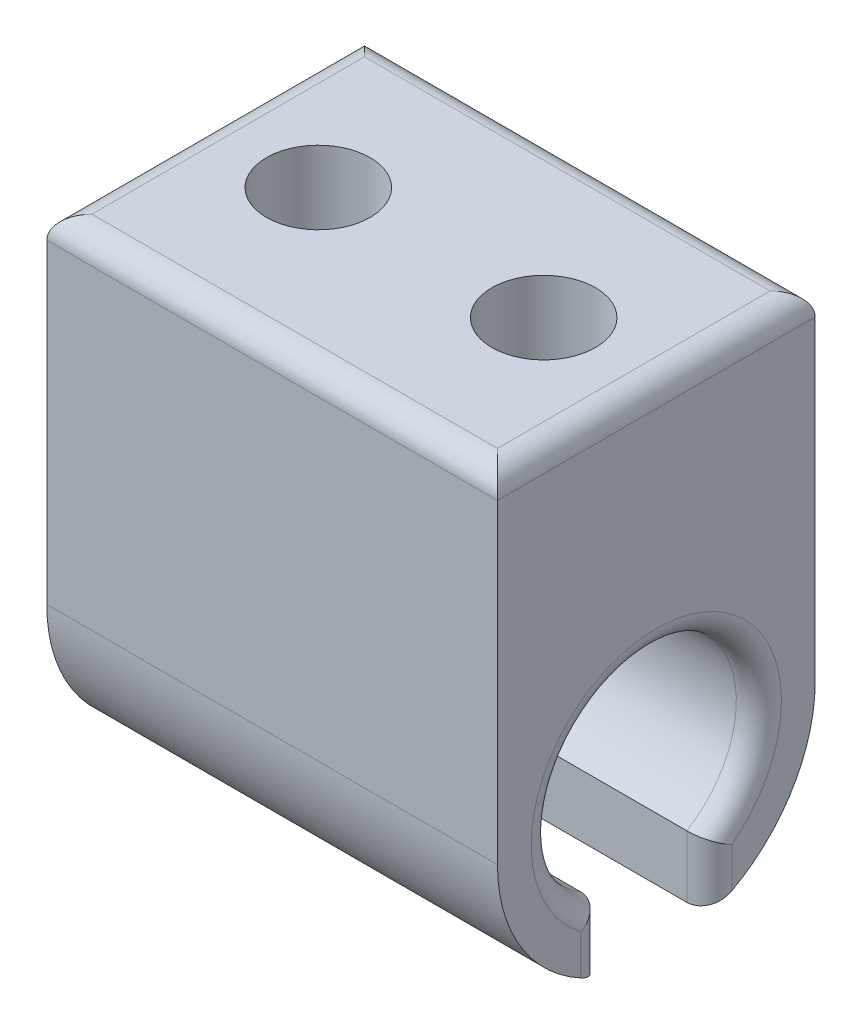
SolidWorks part; units mm, degrees
ref_plane "Front Plane" through (0, 0, 0) normal (0, 0, 1) x (1, 0, 0)
ref_plane "Top Plane" through (0, 0, 0) normal (0, 1, 0) x (1, 0, 0)
ref_plane "Right Plane" through (0, 0, 0) normal (1, 0, 0) x (0, 0, -1)
sketch "Sketch1" plane through (0, 0, 0) normal (1, 0, 0) x (0, 0, -1)
  line L2 (-8.9535, 0) -> (-8.9535, 19.05)
  line L3 (-8.9535, 19.05) -> (8.9535, 19.05)
  line L4 (8.9535, 0) -> (8.9535, 19.05)
  circle A0 centre (0, 0) radius 8.9535
  circle A1 centre (0, 0) radius 5.7785
  dimension "D2" = 11.557
  dimension "D3" = 19.05
  dimension "D1" = 3.175
extrude "Boss-Extrude1" add sketch "Sketch1" along normal blind 25.4
sketch "Sketch2" plane through (0, 19.05, 0) normal (0, 1, 0) x (1, 0, 0)
  line L1 (0, -8.9535) -> (0, 8.9535) construction
  circle A0 centre (6.35, 0) radius 2.921
  circle A1 centre (19.05, 0) radius 2.921
  point P11 (0, 0)
  dimension "D1" = 5.842
  dimension "D2" = 6.35
  dimension "D3" = 12.7
extrude "Cut-Extrude1" cut sketch "Sketch2" against normal up to surface (27.5136 mm away)
sketch "Sketch3" plane through (0, 0, 0) normal (-1, 0, 0) x (0, 0, 1)
  line L1 (-2.9845, -8.9535) -> (2.9845, -8.9535)
  line L2 (-2.9845, -8.9535) -> (-2.9845, -4.9481)
  line L3 (-2.9845, -4.9481) -> (2.9845, -4.9481)
  line L4 (2.9845, -8.9535) -> (2.9845, -4.9481)
  circle A0 centre (0, 0) radius 5.7785 construction
  arc A1 (-8.9535, 0) -> (8.9535, 0) centre (0, 0) ccw construction
  dimension "D1" = 2.9845
  dimension "D2" = 2.9845
extrude "Cut-Extrude2" cut sketch "Sketch3" against normal through all
fillet "Fillet1" radius 1.27 6 edges at (0, -6.6948, 2.9845) (25.4, -6.6948, 2.9845) (25.4, -6.6948, -2.9845) (0, -6.6948, -2.9845) (25.4, 5.7785, 0) (0, 5.7785, 0)
fillet "Fillet2" radius 1.27 4 edges at (25.4, 19.05, 0) (12.7, 19.05, -8.9535) (12.7, 19.05, 8.9535) (0, 19.05, 0)
